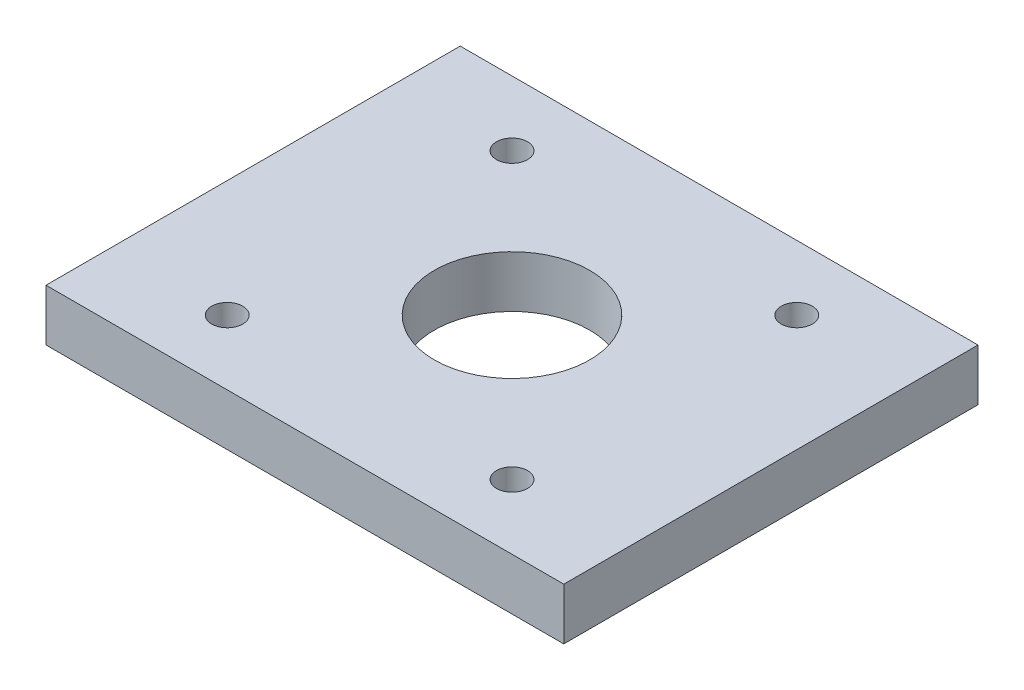
SolidWorks part; units mm, degrees
material "6061-T4 (SS)"
ref_plane "Front Plane" through (0, 0, 0) normal (0, 0, 1) x (1, 0, 0)
ref_plane "Top Plane" through (0, 0, 0) normal (0, 1, 0) x (1, 0, 0)
ref_plane "Right Plane" through (0, 0, 0) normal (1, 0, 0) x (0, 0, -1)
sketch "Sketch1" plane through (0, 0, 0) normal (0, 1, 0) x (1, 0, 0)
  line L1 (100, 80) -> (-100, 80)
  line L2 (100, 80) -> (100, -80)
  line L3 (100, -80) -> (-100, -80)
  line L4 (-100, 80) -> (-100, -80)
  line L5 (100, 80) -> (-100, -80) construction
  line L6 (100, -80) -> (-100, 80) construction
  point P0 (0, 0)
  dimension "D1" = 200
  dimension "D2" = 160
extrude "base" add sketch "Sketch1" along normal blind 20 contours L1 L4 L3 L2
sketch "Sketch2" plane through (0, 20, 0) normal (0, 1, 0) x (1, 0, 0)
  circle A0 centre (0, 0) radius 30
  dimension "D1" = 60
extrude "actuator cut" cut sketch "Sketch2" against normal blind 40
sketch "Sketch3" plane through (0, 20, 0) normal (0, 1, 0) x (1, 0, 0)
  line L1 (57, 67) -> (-57, 67)
  line L2 (67, 57) -> (67, -57)
  line L3 (57, -67) -> (-57, -67)
  line L4 (-67, 57) -> (-67, -57)
  line L5 (67, 67) -> (-67, -67) construction
  line L6 (67, -67) -> (-67, 67) construction
  arc A0 (-57, -67) -> (-67, -57) centre (-57, -57) cw
  arc A1 (67, -57) -> (57, -67) centre (57, -57) cw
  arc A2 (57, 67) -> (67, 57) centre (57, 57) cw
  arc A3 (-57, 67) -> (-67, 57) centre (-57, 57) ccw
  point P0 (0, 0)
  dimension "D2" = 10
  dimension "D3" = 134
  dimension "D4" = 134
split line "Split Line1" [suppressed]
sketch "Sketch4" plane through (0, 20, 0) normal (0, 1, 0) x (1, 0, 0)
  line L1 (55, -55) -> (-55, -55) construction
  line L2 (55, -55) -> (55, 55) construction
  line L3 (55, 55) -> (-55, 55) construction
  line L4 (-55, -55) -> (-55, 55) construction
  line L5 (55, -55) -> (-55, 55) construction
  line L6 (55, 55) -> (-55, -55) construction
  point P0 (0, 0)
  dimension "D1" = 110
  dimension "D2" = 110
hole_wizard "Ø12.0mm Dowel Hole1" positions "3DSketch1" profile "Sketch5" hole size "Ø12.0" standard "ANSI Metric" end condition up to next
sketch3d "3DSketch1"
  point P0 (55, 20, -55)
  point P3 (-55, 20, -55)
  point P6 (-55, 20, 55)
  point P9 (55, 20, 55)
sketch "Sketch5" plane through (55, 20, -55) normal (1, 0, 0) x (0, 0, 1)
  line L0 (0, 0) -> (0, 20)
  line L1 (0, 20) -> (6, 20)
  line L2 (6, 20) -> (6, 0)
  line L5 (6, 0) -> (0, 0)
  line L11 (0, -6.35) -> (0, 107.95) construction
  dimension "Thru Hole Dia." = 12
  dimension "Thru Hole Depth" = 20
sketch "Sketch7" plane through (0, 0, 0) normal (0, -1, 0) x (1, 0, 0)
  circle A0 centre (-55, 55) radius 11
  circle A1 centre (55, 55) radius 11
  circle A2 centre (-55, -55) radius 11
  circle A3 centre (55, -55) radius 11
  dimension "D1" = 22
split line "Split Line2"
